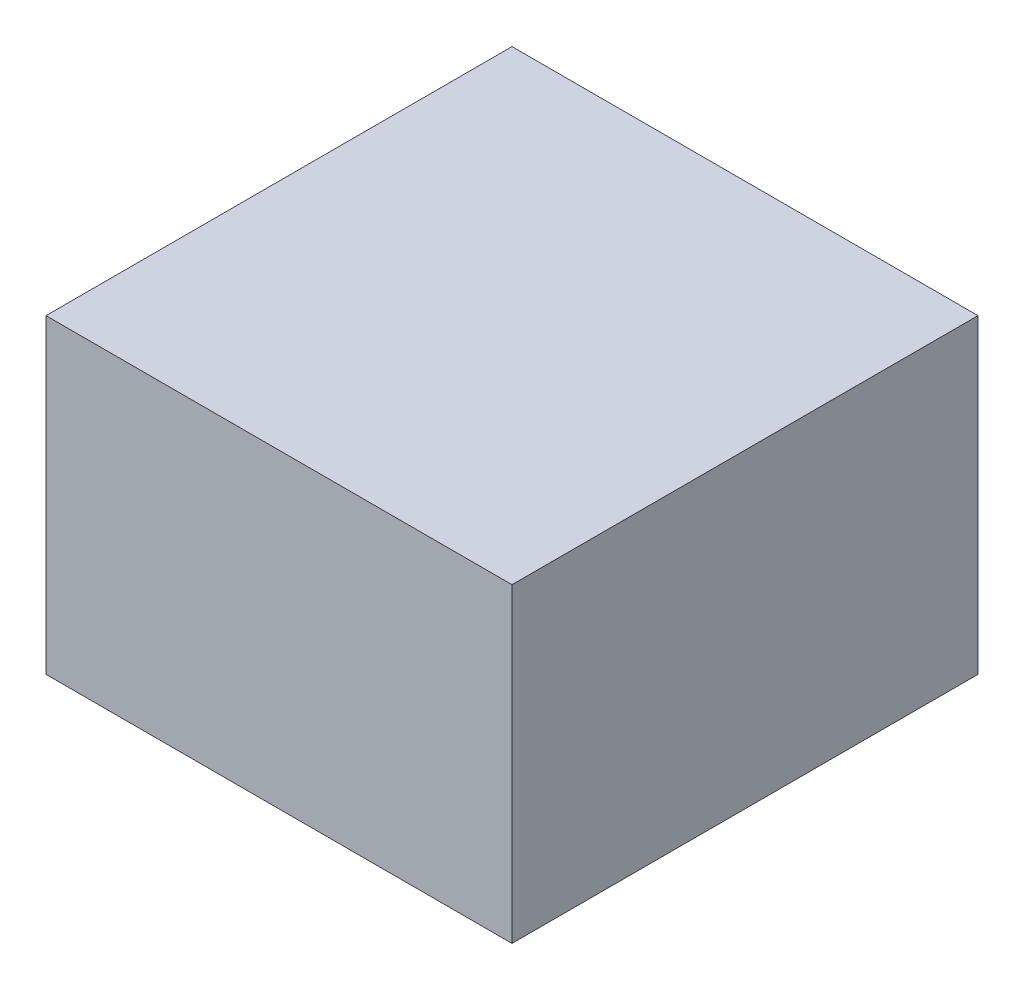
SolidWorks part; units mm, degrees
ref_plane "Front Plane" through (0, 0, 0) normal (0, 0, 1) x (1, 0, 0)
ref_plane "Top Plane" through (0, 0, 0) normal (0, 1, 0) x (1, 0, 0)
ref_plane "Right Plane" through (0, 0, 0) normal (1, 0, 0) x (0, 0, -1)
sketch "Sketch1" plane through (0, 0, 0) normal (0, 0, 1) x (1, 0, 0)
  line L0 (40, 20) -> (-40, 20) construction
  line L1 (25.3958, 20) -> (-34.6042, 20)
  line L2 (25.3958, 20) -> (25.3958, -20)
  line L3 (25.3958, -20) -> (-34.6042, -20)
  line L4 (-34.6042, 20) -> (-34.6042, -20)
  line L5 (-40, -20) -> (40, -20) construction
  dimension "D1" = 60
extrude "Boss-Extrude1" add sketch "Sketch1" along normal blind 60
